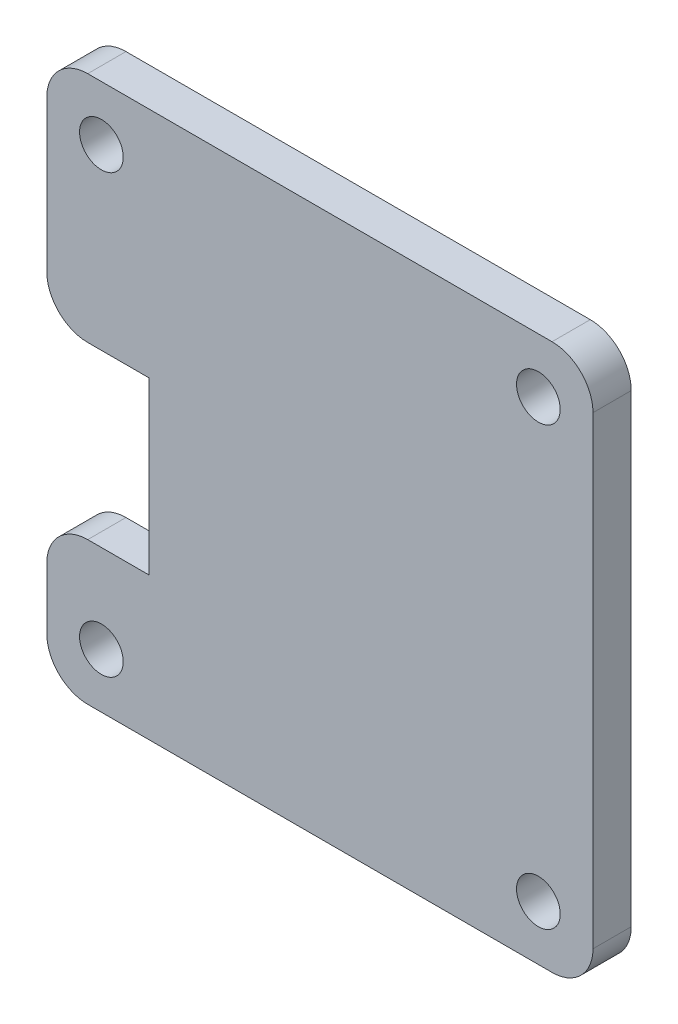
SolidWorks part; units mm, degrees
ref_plane "Front Plane" through (0, 0, 0) normal (0, 0, 1) x (1, 0, 0)
ref_plane "Top Plane" through (0, 0, 0) normal (0, 1, 0) x (1, 0, 0)
ref_plane "Right Plane" through (0, 0, 0) normal (1, 0, 0) x (0, 0, -1)
sketch "Sketch1" plane through (0, 0, 0) normal (0, 0, 1) x (1, 0, 0)
  line L0 (-12.5, -3.3) -> (-20, -3.3) construction
  line L1 (-16, 16) -> (16, 16) construction
  line L2 (-16, 16) -> (-16, -16) construction
  line L3 (-16, -16) -> (16, -16) construction
  line L4 (16, 16) -> (16, -16) construction
  line L5 (-16, 16) -> (16, -16) construction
  line L6 (-16, -16) -> (16, 16) construction
  line L7 (-20, 20) -> (20, 20)
  line L9 (-20, -20) -> (20, -20)
  line L10 (20, 20) -> (20, -20)
  line L11 (-20, 20) -> (20, -20) construction
  line L12 (-20, -20) -> (20, 20) construction
  line L13 (-12.5, -9.55) -> (-12.5, 2.95)
  line L14 (-12.5, 2.95) -> (-20, 2.95)
  line L15 (-20, 2.95) -> (-20, 20)
  line L16 (-12.5, -9.55) -> (-20, -9.55)
  line L17 (-20, -9.55) -> (-20, -20)
  line L18 (-20, 20) -> (-20, 2.95) construction
  line L19 (-20, 2.95) -> (-20, -9.55) construction
  circle A0 centre (-16, 16) radius 1.6
  circle A1 centre (16, 16) radius 1.6
  circle A2 centre (16, -16) radius 1.6
  circle A3 centre (-16, -16) radius 1.6
  point P0 (0, 0)
  point P10 (0, 0)
  point P17 (-20, -3.1581)
  point P20 (-12.5, -3.3)
  dimension "D1" = 3.2
  dimension "D2" = 12.5
  dimension "D3" = 40
  dimension "D4" = 32
  dimension "D5" = 7.5
  dimension "D6" = 10.45
  dimension "D7" = 17.05
extrude "Boss-Extrude1" add sketch "Sketch1" along normal blind 2.8
sketch "Sketch2" plane through (0, 0, 2.8) normal (0, 0, 1) x (1, 0, 0)
  line L0 (-6.4231, -3.3) -> (-12.5, -3.3) construction
  line L2 (-12.5, 2.95) -> (-12.5, -9.55) construction
  line L5 (-10.9231, 8.7) -> (-1.9231, 8.7)
  line L6 (-10.9231, 8.7) -> (-10.9231, -15.3)
  line L7 (-10.9231, -15.3) -> (-1.9231, -15.3)
  line L8 (-1.9231, 8.7) -> (-1.9231, -15.3)
  line L9 (-10.9231, 8.7) -> (-1.9231, -15.3) construction
  line L10 (-10.9231, -15.3) -> (-1.9231, 8.7) construction
  point P2 (-12.5, 0)
  point P5 (-6.4231, -3.3)
  point P7 (-6.4231, -3.0003)
  point P8 (-12.5, -3.3)
  dimension "D1" = 9
  dimension "D2" = 24
extrude "Boss-Extrude2" [suppressed] add sketch "Sketch2" along normal blind 6
fillet "Fillet1" radius 3 6 edges at (-20, -9.55, 1.4) (-20, 2.95, 1.4) (-20, -20, 1.4) (-20, 20, 1.4) (20, -20, 1.4) (20, 20, 1.4)
